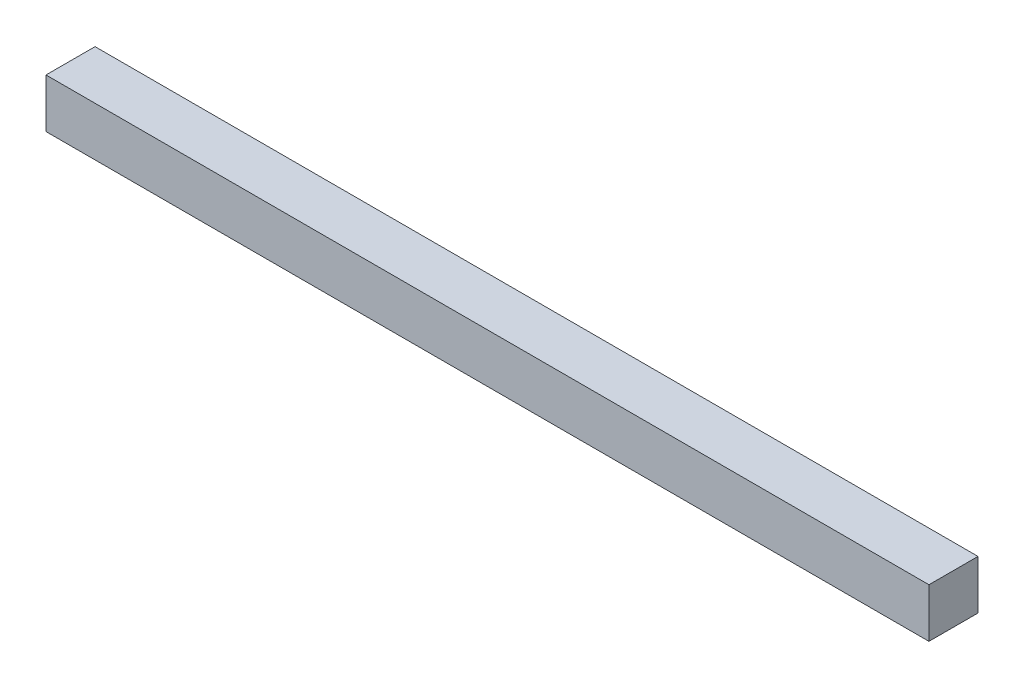
SolidWorks part; units mm, degrees
ref_plane "Front Plane" through (0, 0, 0) normal (0, 0, 1) x (1, 0, 0)
ref_plane "Top Plane" through (0, 0, 0) normal (0, 1, 0) x (1, 0, 0)
ref_plane "Right Plane" through (0, 0, 0) normal (1, 0, 0) x (0, 0, -1)
sketch "Sketch1" plane through (0, 0, 0) normal (1, 0, 0) x (0, 0, -1)
  line L1 (0, 0) -> (25.4, 0)
  line L2 (0, 0) -> (0, 25.4)
  line L3 (0, 25.4) -> (25.4, 25.4)
  line L4 (25.4, 0) -> (25.4, 25.4)
  dimension "D1" = 25.4
  dimension "D2" = 25.4
extrude "Boss-Extrude1" add sketch "Sketch1" along normal blind 457.2
